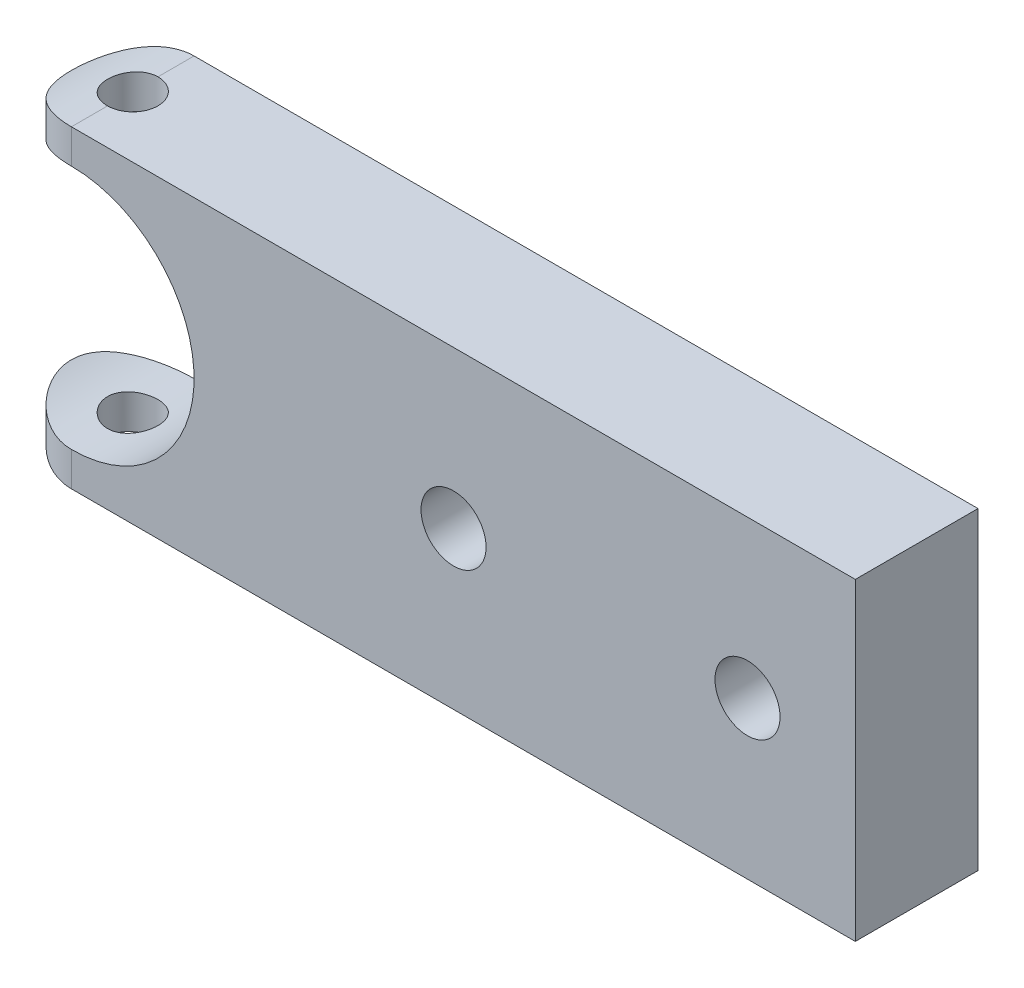
SolidWorks part; units mm, degrees
ref_plane "Front Plane" through (0, 0, 0) normal (0, 0, 1) x (1, 0, 0)
ref_plane "Top Plane" through (0, 0, 0) normal (0, 1, 0) x (1, 0, 0)
ref_plane "Right Plane" through (0, 0, 0) normal (1, 0, 0) x (0, 0, -1)
sketch "Sketch1" plane through (0, 0, 0) normal (0, 0, 1) x (1, 0, 0)
  line L6 (50.8, -20.32) -> (-50.8, -20.32)
  line L7 (50.8, -20.32) -> (50.8, 20.32)
  line L8 (50.8, 20.32) -> (-50.8, 20.32)
  line L10 (50.8, -20.32) -> (-50.8, 20.32) construction
  line L11 (50.8, 20.32) -> (-50.8, -20.32) construction
  arc A2 (-50.8, -20.32) -> (-50.8, 20.32) centre (-50.8, 0) cw
  point P0 (0, 0)
  dimension "D1" = 101.6
  dimension "D2" = 40.64
extrude "Boss-Extrude1" add sketch "Sketch1" along normal blind 15.9004 contours L6 A2 L8 L7
sketch "Sketch2" plane through (2.4816, 0, 15.9004) normal (0, 0, 1) x (1, 0, 0)
  line L0 (48.3184, -20.32) -> (48.3184, 20.32) construction
  circle A0 centre (-53.2816, 0) radius 15.9004
  dimension "D1" = 101.6
extrude "Cut-Extrude1" cut sketch "Sketch2" against normal blind 18.796 and the other way blind 2.54 contours A0
sketch "Sketch3" plane through (0, 0, 0) normal (0, 0, -1) x (-1, 0, 0)
  line L0 (71.12, 0) -> (-50.8, 0) construction
  line L1 (-50.8, -20.32) -> (-50.8, 20.32) construction
  arc A0 (50.8, -20.32) -> (50.8, 20.32) centre (50.8, 0) ccw construction
hole_wizard "CBORE for 5/16 Hex Head Bolt1" positions "Sketch4" profile "Sketch5" counterbore size "5/16" standard "ANSI Inch" end condition through all
sketch "Sketch4" plane through (0, 0, 0) normal (0, 0, -1) x (-1, 0, 0)
  line L0 (71.12, 0) -> (-50.8, 0) construction
  point P0 (-36.83, 0)
  point P4 (1.27, 0)
  dimension "D1" = 13.97
  dimension "D2" = 38.1
sketch "Sketch5" plane through (36.83, 0, 0) normal (1, 0, 0) x (0, 1, 0)
  line L0 (0, 0) -> (0, 15.9004)
  line L1 (0, 15.9004) -> (4.2164, 15.9004)
  line L3 (4.2164, 15.9004) -> (4.2164, 5.969)
  line L4 (4.2164, 5.969) -> (10.3187, 5.969)
  line L5 (10.3187, 5.969) -> (10.3187, 0)
  line L7 (10.3187, 0) -> (0, 0)
  line L11 (0, -6.35) -> (0, 107.95) construction
  dimension "Thru Hole Dia." = 8.4328
  dimension "Thru Hole Depth" = 15.9004
  dimension "C'Bore Dia." = 20.6375
  dimension "C'Bore Depth" = 5.969
sketch "Sketch6" plane through (0, 0, 0) normal (0, 0, -1) x (-1, 0, 0)
  line L0 (50.8, -20.32) -> (50.8, 20.32) construction
hole_wizard "5/16-18 Tapped Hole1" positions "Sketch7" profile "Sketch8" tap size "5/16-18" standard "ANSI Inch" end condition through all
sketch "Sketch7" plane through (0, -20.32, 0) normal (0, -1, 0) x (-1, 0, 0)
  line L0 (50.8, -15.9004) -> (50.8, 0) construction
  point P0 (50.8, -7.9502)
sketch "Sketch8" plane through (-50.8, -20.32, 7.9502) normal (1, 0, 0) x (0, 0, -1)
  line L0 (0, 0) -> (0, 40.64)
  line L1 (0, 40.64) -> (3.2639, 40.64)
  line L2 (3.2639, 40.64) -> (3.2639, 0)
  line L5 (3.2639, 0) -> (0, 0)
  line L11 (0, -6.35) -> (0, 107.95) construction
  dimension "Thru Tap Drill Dia." = 6.5278
  dimension "Thru Tap Drill Depth" = 40.64
cosmetic thread "Hole Thread1" parameters "D2"=7.9375
sketch "Sketch10" plane through (0, -20.32, 0) normal (0, -1, 0) x (1, 0, 0)
  line L1 (-50.8, 15.9004) -> (-71.4681, 15.9004)
  line L3 (-50.8, 0) -> (-71.4681, 0)
  line L4 (-71.4681, 15.9004) -> (-71.4681, 0)
  arc A0 (-50.8, 15.9004) -> (-50.8, 0) centre (-50.8, 7.9502) ccw
extrude "Cut-Extrude2" cut sketch "Sketch10" against normal blind 40.894
sketch "Sketch13" plane through (0, 0, 0) normal (0, 0, -1) x (-1, 0, 0)
  arc A0 (50.8, -20.32) -> (50.8, 20.32) centre (50.8, 0) ccw construction
  dimension "D1" = 20.32
